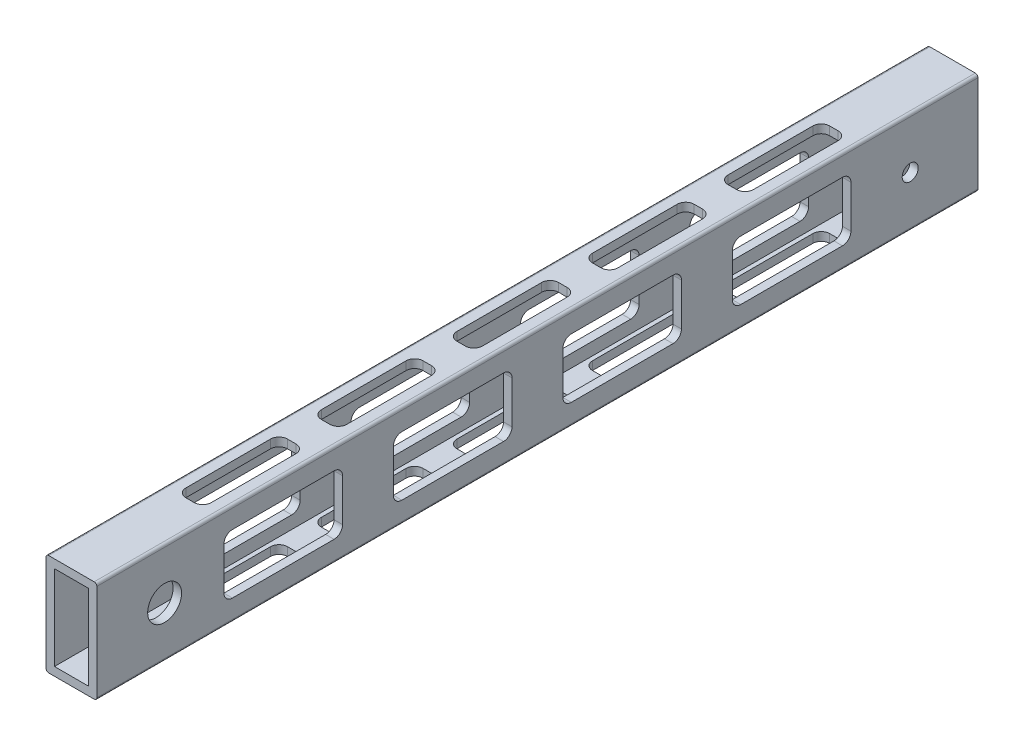
SolidWorks part; units mm, degrees
material "6061-T6 (SS)"
ref_plane "Front Plane" through (0, 0, 0) normal (0, 0, 1) x (1, 0, 0)
ref_plane "Top Plane" through (0, 0, 0) normal (0, 1, 0) x (1, 0, 0)
ref_plane "Right Plane" through (0, 0, 0) normal (1, 0, 0) x (0, 0, -1)
sketch "Sketch1" plane through (0, 0, 0) normal (0, 0, 1) x (1, 0, 0)
  line L0 (-6.35, -15.875) -> (-6.35, 15.875)
  line L1 (-8.525, -19.05) -> (8.525, -19.05)
  line L2 (-9.525, -18.05) -> (-9.525, 18.05)
  line L3 (-8.525, 19.05) -> (8.525, 19.05)
  line L4 (9.525, -18.05) -> (9.525, 18.05)
  line L5 (-9.525, -19.05) -> (9.525, 19.05) construction
  line L6 (-9.525, 19.05) -> (9.525, -19.05) construction
  line L7 (-6.35, 15.875) -> (6.35, 15.875)
  line L8 (6.35, -15.875) -> (6.35, 15.875)
  line L9 (-6.35, -15.875) -> (6.35, -15.875)
  arc A0 (-8.525, -19.05) -> (-9.525, -18.05) centre (-8.525, -18.05) cw
  arc A1 (8.525, -19.05) -> (9.525, -18.05) centre (8.525, -18.05) ccw
  arc A2 (8.525, 19.05) -> (9.525, 18.05) centre (8.525, 18.05) cw
  arc A3 (-9.525, 18.05) -> (-8.525, 19.05) centre (-8.525, 18.05) cw
  arc A4 (-6.35, 15.875) -> (-6.35, 15.875) centre (-6.35, 15.875) cw
  arc A5 (6.35, 15.875) -> (6.35, 15.875) centre (6.35, 15.875) cw
  arc A6 (6.35, -15.875) -> (6.35, -15.875) centre (6.35, -15.875) ccw
  arc A7 (-6.35, -15.875) -> (-6.35, -15.875) centre (-6.35, -15.875) cw
  point P0 (0, 0)
  dimension "D3" = 1
  dimension "D1" = 19.05
  dimension "D2" = 38.1
  dimension "D4" = 3.175
extrude "Boss-Extrude1" add sketch "Sketch1" along normal mid plane 330.2
sketch "Sketch2" plane through (0, 19.05, 0) normal (0, 1, 0) x (1, 0, 0)
  line L0 (-4.7625, -66.675) -> (-4.7625, -34.925)
  line L1 (-1.5875, -120.65) -> (1.5875, -120.65)
  line L2 (-4.7625, -117.475) -> (-4.7625, -85.725)
  line L3 (-1.5875, -82.55) -> (1.5875, -82.55)
  line L4 (4.7625, -117.475) -> (4.7625, -85.725)
  line L5 (-4.7625, -120.65) -> (4.7625, -82.55) construction
  line L6 (-4.7625, -82.55) -> (4.7625, -120.65) construction
  line L7 (-1.5875, -69.85) -> (1.5875, -69.85)
  line L8 (4.7625, -66.675) -> (4.7625, -34.925)
  line L9 (-1.5875, -31.75) -> (1.5875, -31.75)
  line L10 (-4.7625, -15.875) -> (-4.7625, 15.875)
  line L11 (-1.5875, -19.05) -> (1.5875, -19.05)
  line L12 (4.7625, -15.875) -> (4.7625, 15.875)
  line L13 (-1.5875, 19.05) -> (1.5875, 19.05)
  line L14 (-4.7625, 34.925) -> (-4.7625, 66.675)
  line L15 (-1.5875, 31.75) -> (1.5875, 31.75)
  line L16 (4.7625, 34.925) -> (4.7625, 66.675)
  line L17 (-1.5875, 69.85) -> (1.5875, 69.85)
  line L18 (-4.7625, 85.725) -> (-4.7625, 117.475)
  line L19 (-1.5875, 82.55) -> (1.5875, 82.55)
  line L20 (4.7625, 85.725) -> (4.7625, 117.475)
  line L21 (-1.5875, 120.65) -> (1.5875, 120.65)
  line L22 (0, -101.6) -> (0, -50.8) construction
  arc A0 (-1.5875, -120.65) -> (-4.7625, -117.475) centre (-1.5875, -117.475) cw
  arc A1 (1.5875, -120.65) -> (4.7625, -117.475) centre (1.5875, -117.475) ccw
  arc A2 (1.5875, -82.55) -> (4.7625, -85.725) centre (1.5875, -85.725) cw
  arc A3 (-4.7625, -85.725) -> (-1.5875, -82.55) centre (-1.5875, -85.725) cw
  arc A4 (-4.7625, -34.925) -> (-1.5875, -31.75) centre (-1.5875, -34.925) cw
  arc A5 (-1.5875, -69.85) -> (-4.7625, -66.675) centre (-1.5875, -66.675) cw
  arc A6 (1.5875, -69.85) -> (4.7625, -66.675) centre (1.5875, -66.675) ccw
  arc A7 (1.5875, -31.75) -> (4.7625, -34.925) centre (1.5875, -34.925) cw
  arc A8 (-4.7625, 15.875) -> (-1.5875, 19.05) centre (-1.5875, 15.875) cw
  arc A9 (-1.5875, -19.05) -> (-4.7625, -15.875) centre (-1.5875, -15.875) cw
  arc A10 (1.5875, -19.05) -> (4.7625, -15.875) centre (1.5875, -15.875) ccw
  arc A11 (1.5875, 19.05) -> (4.7625, 15.875) centre (1.5875, 15.875) cw
  arc A12 (-4.7625, 66.675) -> (-1.5875, 69.85) centre (-1.5875, 66.675) cw
  arc A13 (-1.5875, 31.75) -> (-4.7625, 34.925) centre (-1.5875, 34.925) cw
  arc A14 (1.5875, 31.75) -> (4.7625, 34.925) centre (1.5875, 34.925) ccw
  arc A15 (1.5875, 69.85) -> (4.7625, 66.675) centre (1.5875, 66.675) cw
  arc A16 (-4.7625, 117.475) -> (-1.5875, 120.65) centre (-1.5875, 117.475) cw
  arc A17 (-1.5875, 82.55) -> (-4.7625, 85.725) centre (-1.5875, 85.725) cw
  arc A18 (1.5875, 82.55) -> (4.7625, 85.725) centre (1.5875, 85.725) ccw
  arc A19 (1.5875, 120.65) -> (4.7625, 117.475) centre (1.5875, 117.475) cw
  point P0 (0, -101.6)
  point P20 (0, -50.8)
  point P33 (0, 0)
  point P46 (0, 50.8)
  point P59 (0, 101.6)
  dimension "D3" = 3.175
  dimension "D1" = 9.525
  dimension "D2" = 38.1
  dimension "D5" = 50.8
  dimension "D4" = 5
extrude "Cut-Extrude1" cut sketch "Sketch2" against normal through all both and the other way through all
sketch "Sketch3" plane through (9.525, 0, 0) normal (1, 0, 0) x (0, 0, -1)
  line L0 (-53.975, -7.9375) -> (-53.975, 7.9375)
  line L1 (-114.3, -11.1125) -> (-76.2, -11.1125)
  line L2 (-117.475, -7.9375) -> (-117.475, 7.9375)
  line L3 (-114.3, 11.1125) -> (-76.2, 11.1125)
  line L4 (-73.025, -7.9375) -> (-73.025, 7.9375)
  line L5 (-117.475, -11.1125) -> (-73.025, 11.1125) construction
  line L6 (-117.475, 11.1125) -> (-73.025, -11.1125) construction
  line L7 (-50.8, -11.1125) -> (-12.7, -11.1125)
  line L8 (-9.525, -7.9375) -> (-9.525, 7.9375)
  line L9 (-50.8, 11.1125) -> (-12.7, 11.1125)
  line L10 (9.525, -7.9375) -> (9.525, 7.9375)
  line L11 (12.7, -11.1125) -> (50.8, -11.1125)
  line L12 (53.975, -7.9375) -> (53.975, 7.9375)
  line L13 (12.7, 11.1125) -> (50.8, 11.1125)
  line L14 (-95.25, 0) -> (-31.75, 0) construction
  line L15 (73.025, -7.9375) -> (73.025, 7.9375)
  line L16 (76.2, -11.1125) -> (114.3, -11.1125)
  line L17 (117.475, -7.9375) -> (117.475, 7.9375)
  line L18 (76.2, 11.1125) -> (114.3, 11.1125)
  line L19 (31.75, 0) -> (95.25, 0) construction
  line L28 (-31.75, 0) -> (31.75, 0) construction
  arc A0 (-114.3, -11.1125) -> (-117.475, -7.9375) centre (-114.3, -7.9375) cw
  arc A1 (-76.2, -11.1125) -> (-73.025, -7.9375) centre (-76.2, -7.9375) ccw
  arc A2 (-76.2, 11.1125) -> (-73.025, 7.9375) centre (-76.2, 7.9375) cw
  arc A3 (-117.475, 7.9375) -> (-114.3, 11.1125) centre (-114.3, 7.9375) cw
  arc A4 (-53.975, 7.9375) -> (-50.8, 11.1125) centre (-50.8, 7.9375) cw
  arc A5 (-50.8, -11.1125) -> (-53.975, -7.9375) centre (-50.8, -7.9375) cw
  arc A6 (-12.7, -11.1125) -> (-9.525, -7.9375) centre (-12.7, -7.9375) ccw
  arc A7 (-12.7, 11.1125) -> (-9.525, 7.9375) centre (-12.7, 7.9375) cw
  arc A8 (9.525, 7.9375) -> (12.7, 11.1125) centre (12.7, 7.9375) cw
  arc A9 (12.7, -11.1125) -> (9.525, -7.9375) centre (12.7, -7.9375) cw
  arc A10 (50.8, -11.1125) -> (53.975, -7.9375) centre (50.8, -7.9375) ccw
  arc A11 (50.8, 11.1125) -> (53.975, 7.9375) centre (50.8, 7.9375) cw
  arc A12 (73.025, 7.9375) -> (76.2, 11.1125) centre (76.2, 7.9375) cw
  arc A13 (76.2, -11.1125) -> (73.025, -7.9375) centre (76.2, -7.9375) cw
  arc A14 (114.3, -11.1125) -> (117.475, -7.9375) centre (114.3, -7.9375) ccw
  arc A15 (114.3, 11.1125) -> (117.475, 7.9375) centre (114.3, 7.9375) cw
  point P0 (-95.25, 0)
  point P19 (95.25, 0)
  point P20 (-31.75, 0)
  point P33 (31.75, 0)
  point P60 (0, 0)
  dimension "D3" = 3.175
  dimension "D1" = 22.225
  dimension "D2" = 44.45
  dimension "D5" = 63.5
  dimension "D4" = 4
extrude "Cut-Extrude2" cut sketch "Sketch3" against normal through all both and the other way through all
sketch "Sketch4" plane through (9.525, 0, 0) normal (1, 0, 0) x (0, 0, -1)
  line L0 (-165.1, -18.05) -> (-165.1, 18.05) construction
  line L2 (-139.7, 0) -> (-165.1, 0) construction
  line L3 (-139.7, 0) -> (-139.7, 19.05) construction
  line L4 (165.1, 0) -> (139.7, 0) construction
  line L5 (165.1, -18.05) -> (165.1, 18.05) construction
  line L6 (139.7, 0) -> (139.7, 19.05) construction
  line L7 (-165.1, 19.05) -> (165.1, 19.05) construction
  circle A0 centre (-139.7, 0) radius 6.35
  circle A1 centre (139.7, 0) radius 3
  dimension "D1" = 12.7
  dimension "D4" = 6
  dimension "D2" = 19.05
  dimension "D3" = 25.4
extrude "Cut-Extrude3" cut sketch "Sketch4" against normal through all both and the other way through all
